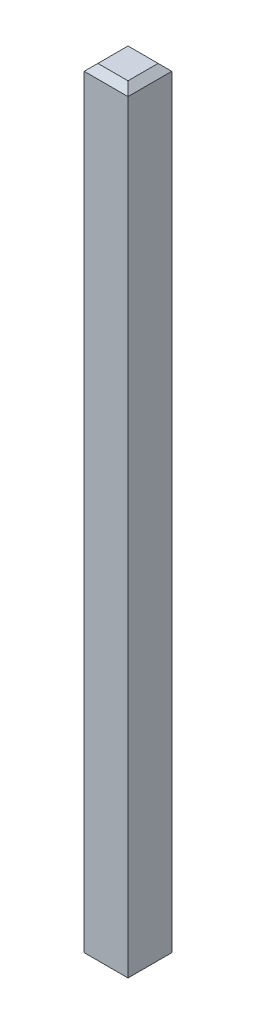
SolidWorks part; units mm, degrees
ref_plane "Front" through (0, 0, 0) normal (0, 0, 1) x (1, 0, 0)
ref_plane "Top" through (0, 0, 0) normal (0, 1, 0) x (1, 0, 0)
ref_plane "Right" through (0, 0, 0) normal (1, 0, 0) x (0, 0, -1)
sketch "Эскиз1" plane through (0, 0, 0) normal (0, 1, 0) x (1, 0, 0)
  line L1 (-0.32, 0.32) -> (0.32, 0.32)
  line L2 (-0.32, 0.32) -> (-0.32, -0.32)
  line L3 (-0.32, -0.32) -> (0.32, -0.32)
  line L4 (0.32, 0.32) -> (0.32, -0.32)
  line L5 (-0.32, 0.32) -> (0.32, -0.32) construction
  line L6 (-0.32, -0.32) -> (0.32, 0.32) construction
  point P0 (0, 0)
  dimension "D1" = 0.64
  dimension "D2" = 0.64
sketch "Эскиз2" plane through (0, 0, 0) normal (0, 0, 1) x (1, 0, 0)
  line L0 (0, 0) -> (0, 11.35)
  point P6 (0, 11.35)
  dimension "D1" = 11.35
sweep "По траектории1" add profiles "Эскиз1" path "Эскиз2"
chamfer "Фаска1" distance 0.1 angle 45 8 edges at (0, 0, -0.32) (-0.32, 0, 0) (0, 0, 0.32) (0.32, 0, 0) (0, 11.35, -0.32) (0, 11.35, 0.32) (-0.32, 11.35, 0) (0.32, 11.35, 0)
equation "\"D2@Эскиз1\"=\"D1@Эскиз1\""
